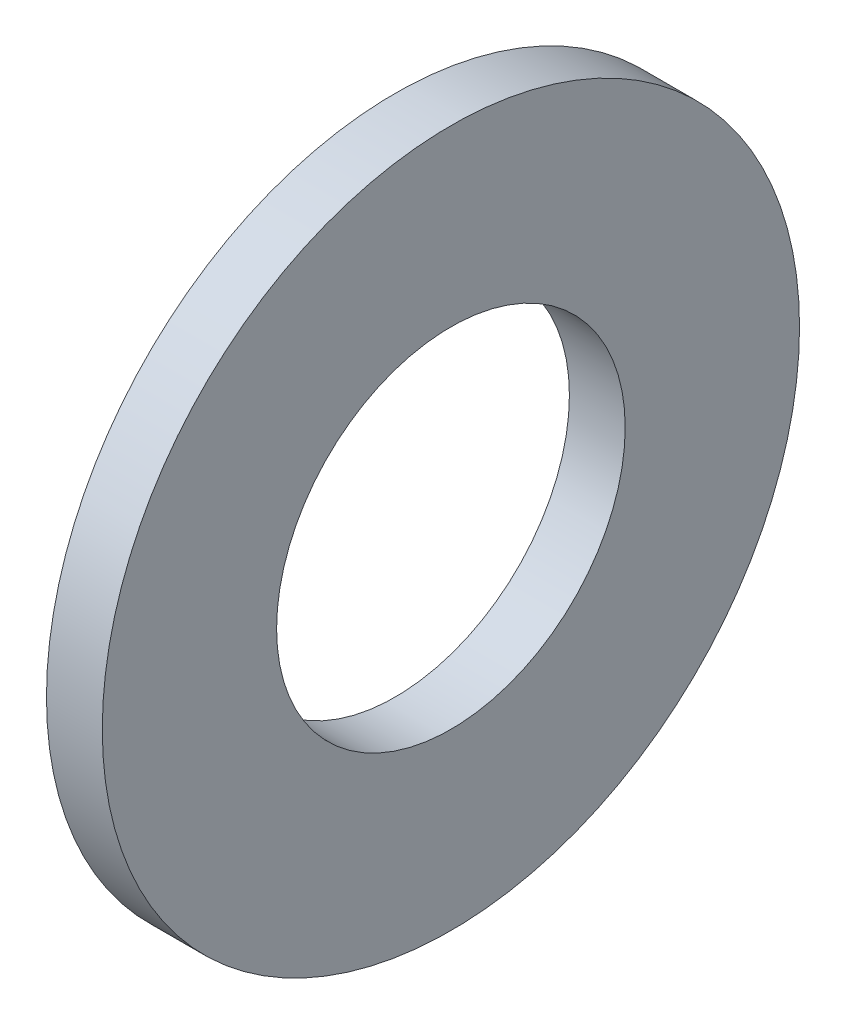
SolidWorks part; units mm, degrees
ref_plane "Front Plane" through (0, 0, 0) normal (0, 0, 1) x (1, 0, 0)
ref_plane "Top Plane" through (0, 0, 0) normal (0, 1, 0) x (1, 0, 0)
ref_plane "Right Plane" through (0, 0, 0) normal (1, 0, 0) x (0, 0, -1)
sketch "Sketch1" plane through (0, 0, 0) normal (1, 0, 0) x (0, 0, -1)
  circle A0 centre (0, 0) radius 0.203
  circle A1 centre (0, 0) radius 0.406
  dimension "D1" = 0.406
  dimension "D2" = 0.812
extrude "Boss-Extrude1" add sketch "Sketch1" along normal mid plane 0.065
